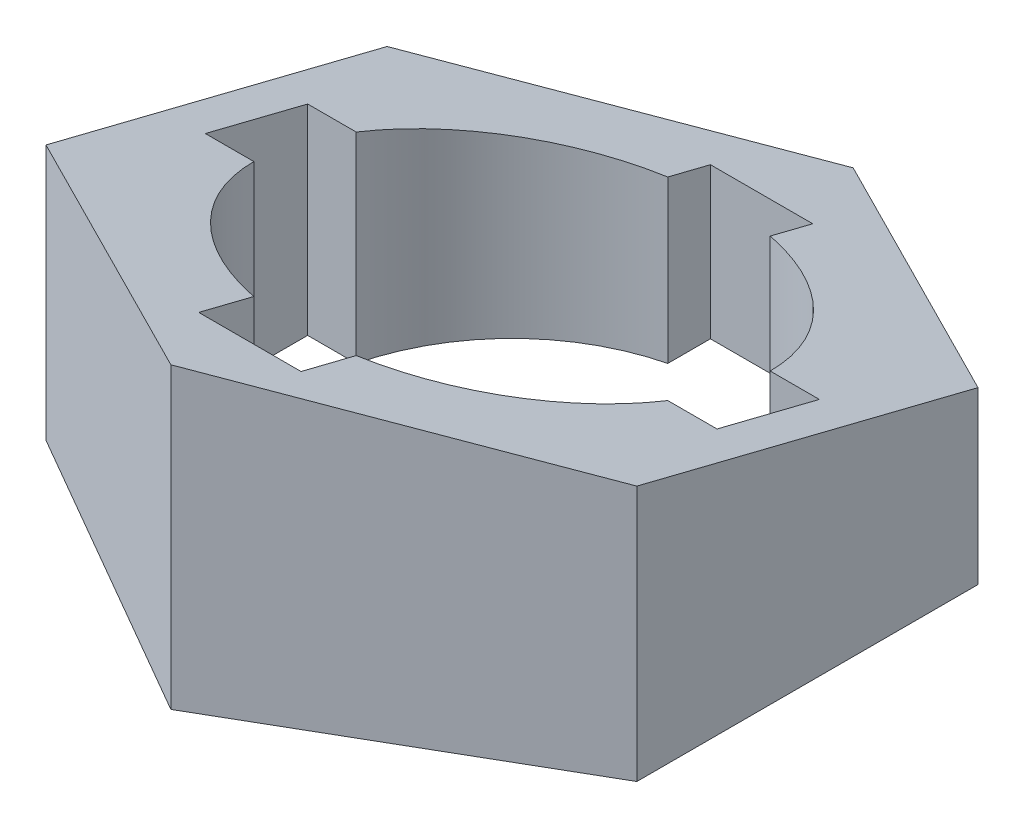
SolidWorks part; units mm, degrees
material "Plain Carbon Steel"
ref_plane "Front Plane" through (0, 0, 0) normal (0, 0, 1) x (1, 0, 0)
ref_plane "Top Plane" through (0, 0, 0) normal (0, 1, 0) x (1, 0, 0)
ref_plane "Right Plane" through (0, 0, 0) normal (1, 0, 0) x (0, 0, -1)
sketch "Sketch1" plane through (0, 0, 0) normal (0, 1, 0) x (1, 0, 0)
  line L1 (0, 40) -> (-34.641, 20)
  line L2 (-34.641, 20) -> (-34.641, -20)
  line L3 (-34.641, -20) -> (0, -40)
  line L4 (0, -40) -> (34.641, -20)
  line L5 (34.641, -20) -> (34.641, 20)
  line L6 (34.641, 20) -> (0, 40)
  circle A0 centre (0, 0) radius 34.641 construction
  dimension "D1" = 80
extrude "Boss-Extrude2" add sketch "Sketch1" along normal blind 35 contours L1 L2 L3 L4 L5 L6
ref_plane "Plane1" through (-34.641, 0, 0) normal (-1, 0, 0) x (0, 0, 1)
ref_plane "Plane3" through (0, 35, 0) normal (0, 1, 0) x (1, 0, 0)
sketch "Sketch8" plane through (0, 35, 0) normal (0, 1, 0) x (1, 0, 0)
  line L1 (-6, 29.266) -> (6, 29.266)
  line L2 (-6, 29.266) -> (-6, 24.2693)
  line L4 (6, 29.266) -> (6, 24.2693)
  line L6 (34.641, 20) -> (0, 40)
  line L7 (0, 40) -> (-34.641, 20)
  line L8 (-34.641, 20) -> (-34.641, -20)
  line L9 (-34.641, -20) -> (0, -40)
  line L10 (0, -40) -> (34.641, -20)
  line L11 (34.641, -20) -> (34.641, 20)
  line L12 (34.641, 20) -> (0, 40)
  line L13 (0, 40) -> (-34.641, 20)
  line L14 (-34.641, 20) -> (-34.641, -20)
  line L15 (-34.641, -20) -> (0, -40)
  line L16 (0, -40) -> (34.641, -20)
  line L17 (34.641, -20) -> (34.641, 20)
  line L19 (30.0404, 6) -> (24.2693, 6)
  line L20 (30.0404, 6) -> (30.0404, -6)
  line L21 (30.0404, -6) -> (24.2693, -6)
  line L25 (-6, -30.734) -> (6, -30.734)
  line L26 (-6, -30.734) -> (-6, -24.2693)
  line L28 (6, -30.734) -> (6, -24.2693)
  line L31 (-29.9596, -6) -> (-24.2693, -6)
  line L32 (-29.9596, -6) -> (-29.9596, 6)
  line L33 (-29.9596, 6) -> (-24.2693, 6)
  arc A0 (-6, 24.2693) -> (-24.2693, 6) centre (0, 0) ccw
  arc A1 (-24.2693, -6) -> (-6, -24.2693) centre (0, 0) ccw
  arc A2 (6, -24.2693) -> (24.2693, -6) centre (0, 0) ccw
  arc A3 (24.2693, 6) -> (6, 24.2693) centre (0, 0) ccw
  point P6 (0, 25)
  point P14 (25, 0)
  point P19 (0, -25)
  point P24 (-25, 0)
  dimension "D2" = 50
  dimension "D3" = 12
  dimension "D4" = 12
  dimension "D5" = 12
  dimension "D6" = 12
  dimension "D7" = 60
  dimension "D8" = 60
  dimension "D1" = 0
extrude "Cut-Extrude8" cut sketch "Sketch8" against normal through all both contours L28 A2 L21 L20 L19 A3 L4 L1 L2 A0 L33 L32 L31 A1 L26 L25
sketch "Sketch9" plane through (-34.641, 0, 0) normal (-1, 0, 0) x (0, 0, 1)
  line L2 (40, 35) -> (20, 35) construction
  line L4 (-20, 0) -> (20, 0)
  line L5 (20, 0) -> (20, 35)
  line L6 (20, 35) -> (-20, 35)
  line L7 (-20, 35) -> (-20, 0)
  line L10 (20, 35) -> (-20, 35)
  line L14 (-20, 35) -> (-40, 35) construction
  line L15 (-40, 35) -> (-40, 0) construction
  line L18 (40, 35) -> (20, 35)
  line L22 (-20, 35) -> (-40, 35)
  line L23 (-40, 35) -> (-40, 15)
  line L24 (40, 35) -> (-40, 15)
  line L25 (-40, 15) -> (-40, 35)
  dimension "D2" = 20
  dimension "D1" = 0
extrude "Cut-Extrude10" cut sketch "Sketch9" against normal through all both contours L24 L18 L10 L22 L23
